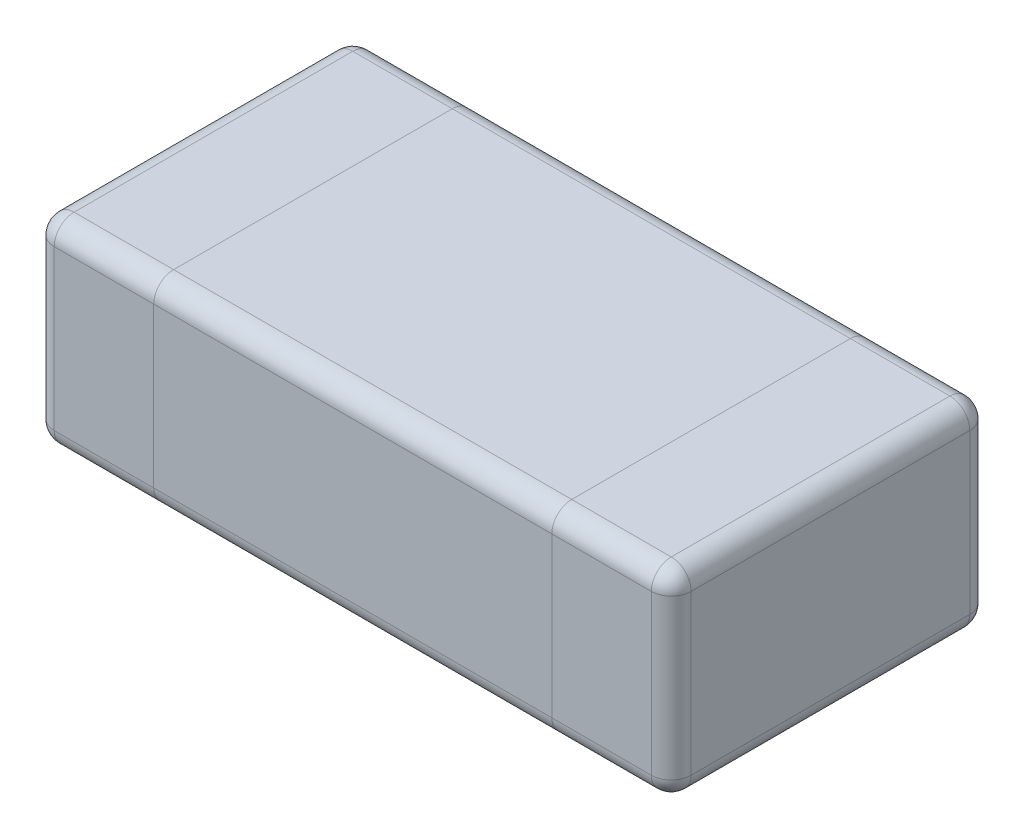
SolidWorks part; units mm, degrees
ref_plane "Front Plane" through (0, 0, 0) normal (0, 0, 1) x (1, 0, 0)
ref_plane "Top Plane" through (0, 0, 0) normal (0, 1, 0) x (1, 0, 0)
ref_plane "Right Plane" through (0, 0, 0) normal (1, 0, 0) x (0, 0, -1)
sketch "Sketch1" plane through (0, 0, 0) normal (0, 1, 0) x (1, 0, 0)
  line L1 (0, 0) -> (0.3, 0)
  line L2 (0, 0) -> (0, 0.8)
  line L3 (0, 0.8) -> (0.3, 0.8)
  line L4 (0.3, 0) -> (0.3, 0.8)
  line L5 (0.15, 0.8) -> (0.15, 0) construction
  line L6 (0, 0.4) -> (0.3, 0.4) construction
  line L7 (1.3, 0.8) -> (1.6, 0.8)
  line L8 (1.3, 0.8) -> (1.3, 0)
  line L9 (1.3, 0) -> (1.6, 0)
  line L10 (1.6, 0.8) -> (1.6, 0)
  line L11 (1.45, 0) -> (1.45, 0.8) construction
  line L12 (1.3, 0.4) -> (1.6, 0.4) construction
  point P112 (0.15, 0.4)
  point P158 (1.45, 0.4)
  dimension "D1" = 0.8
  dimension "D2" = 0.8
  dimension "D3" = 1.6
  dimension "D4" = 0.3
  dimension "D5" = 0.3
extrude "Boss-Extrude1" add sketch "Sketch1" along normal blind 0.5
sketch "Sketch2" plane through (0, 0, 0) normal (0, 1, 0) x (1, 0, 0)
  line L1 (0.3, 0.8) -> (1.3, 0.8)
  line L2 (0.3, 0.8) -> (0.3, 0)
  line L3 (0.3, 0) -> (1.3, 0)
  line L4 (1.3, 0.8) -> (1.3, 0)
  line L5 (0.8, 0) -> (0.8, 0.8) construction
  line L6 (0.3, 0.4) -> (1.3, 0.4) construction
  point P132 (0.8, 0.4)
extrude "Boss-Extrude2" add sketch "Sketch2" along normal blind 0.5 separate body
fillet "Fillet1" radius 0.05 8 edges at (0, 0.25, -0.8) (0, 0.5, -0.4) (0, 0.25, 0) (0, 0, -0.4) (0.15, 0, -0.8) (0.15, 0, 0) (0.15, 0.5, -0.8) (0.15, 0.5, 0)
fillet "Fillet2" radius 0.05 8 edges at (1.6, 0.25, 0) (1.6, 0.5, -0.4) (1.6, 0.25, -0.8) (1.6, 0, -0.4) (1.45, 0, 0) (1.45, 0.5, 0) (1.45, 0, -0.8) (1.45, 0.5, -0.8)
fillet "Fillet3" radius 0.05 4 edges at (0.8, 0, 0) (0.8, 0, -0.8) (0.8, 0.5, -0.8) (0.8, 0.5, 0)
